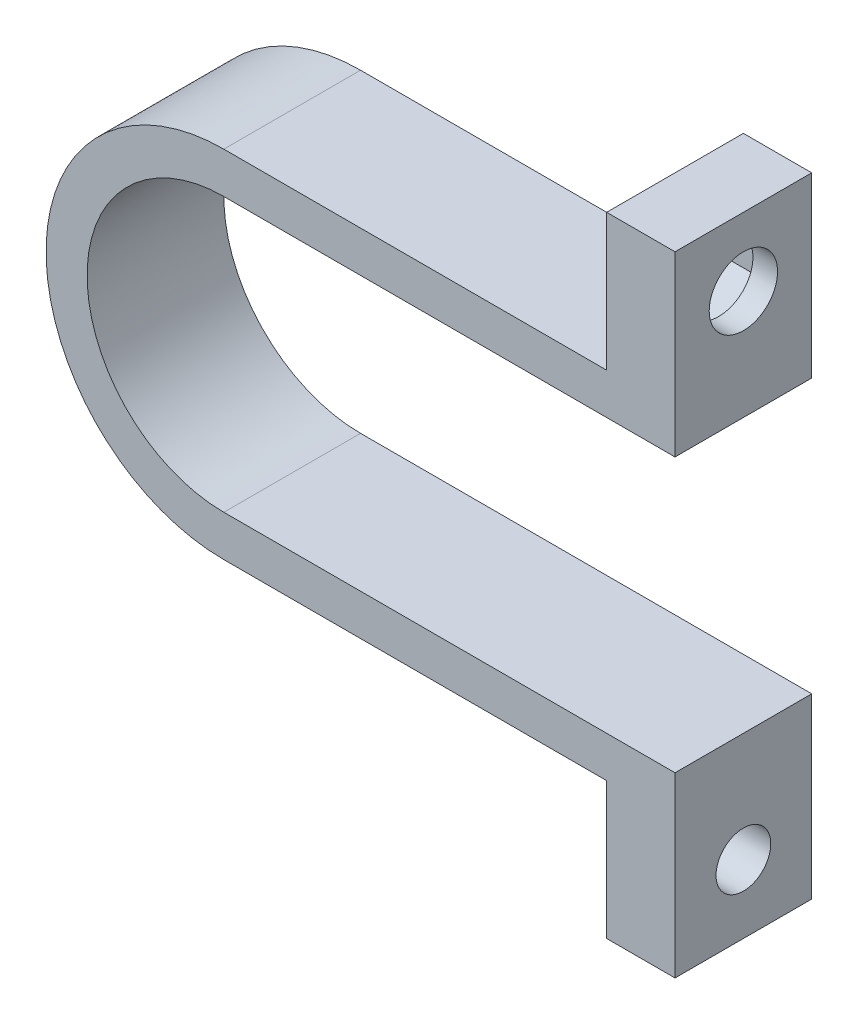
SolidWorks part; units mm, degrees
ref_plane "前视基准面" through (0, 0, 0) normal (0, 0, 1) x (1, 0, 0)
ref_plane "上视基准面" through (0, 0, 0) normal (0, 1, 0) x (1, 0, 0)
ref_plane "右视基准面" through (0, 0, 0) normal (1, 0, 0) x (0, 0, -1)
sketch "草图1" plane through (0, 0, 0) normal (0, 0, 1) x (1, 0, 0)
  line L0 (0, 13) -> (28, 13)
  line L1 (28, 13) -> (28, 23)
  line L2 (28, 23) -> (33, 23)
  line L3 (33, 23) -> (33, 10)
  line L4 (33, 10) -> (0, 10)
  line L5 (0, 0) -> (26.4825, 0) construction
  line L6 (28, -23) -> (33, -23)
  line L7 (28, -13) -> (28, -23)
  line L8 (33, -23) -> (33, -10)
  line L9 (33, -10) -> (0, -10)
  line L10 (0, -13) -> (28, -13)
  arc A0 (0, 10) -> (0, -10) centre (0, 0) ccw
  arc A1 (0, 13) -> (0, -13) centre (0, 0) ccw
  dimension "D1" = 10
  dimension "D2" = 13
  dimension "D3" = 10
  dimension "D4" = 5
  dimension "D6" = 28
extrude "凸台-拉伸1" add sketch "草图1" along normal blind 10
sketch "草图2" plane through (28, 0, 0) normal (-1, 0, 0) x (0, 0, 1)
  line L0 (0, 13) -> (10, 23) construction
  line L1 (0, 23) -> (0, 13) construction
  line L2 (8.5, 15.9793) -> (8.5, 20.0207)
  line L3 (8.5, 20.0207) -> (5, 22.0415)
  line L4 (5, 22.0415) -> (1.5, 20.0207)
  line L5 (1.5, 20.0207) -> (1.5, 15.9793)
  line L6 (1.5, 15.9793) -> (5, 13.9585)
  line L7 (5, 13.9585) -> (8.5, 15.9793)
  circle A0 centre (5, 18) radius 3.5 construction
  dimension "D1" = 7
extrude "切除-拉伸1" cut sketch "草图2" against normal blind 3.2
sketch "草图3" plane through (28, 0, 0) normal (-1, 0, 0) x (0, 0, 1)
  line L0 (0, 13) -> (10, 23) construction
  circle A0 centre (5, 18) radius 2.5
  dimension "D1" = 5
extrude "切除-拉伸2" cut sketch "草图3" against normal through all
sketch "草图4" plane through (28, 0, 0) normal (-1, 0, 0) x (0, 0, 1)
  line L0 (0, -23) -> (10, -13) construction
  circle A0 centre (5, -18) radius 2
extrude "切除-拉伸3" cut sketch "草图4" against normal through all
